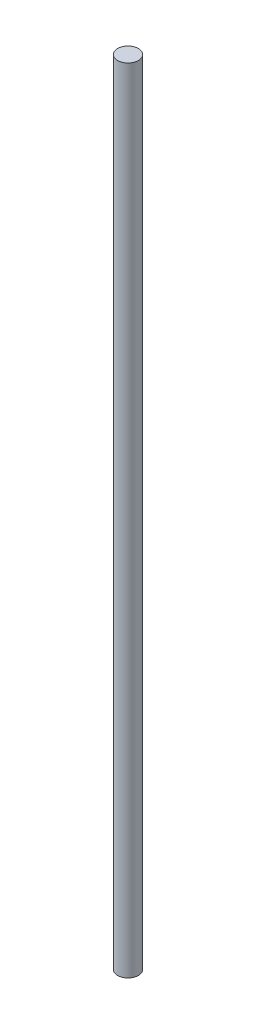
SolidWorks part; units mm, degrees
material "Chrome Stainless Steel"
ref_plane "Front Plane" through (0, 0, 0) normal (0, 0, 1) x (1, 0, 0)
ref_plane "Top Plane" through (0, 0, 0) normal (0, 1, 0) x (1, 0, 0)
ref_plane "Right Plane" through (0, 0, 0) normal (1, 0, 0) x (0, 0, -1)
sketch "Sketch1" plane through (0, 0, 0) normal (0, 1, 0) x (1, 0, 0)
  circle A0 centre (0, 0) radius 4
  dimension "D1" = 8
extrude "Boss-Extrude1" add sketch "Sketch1" along normal blind 304.8
